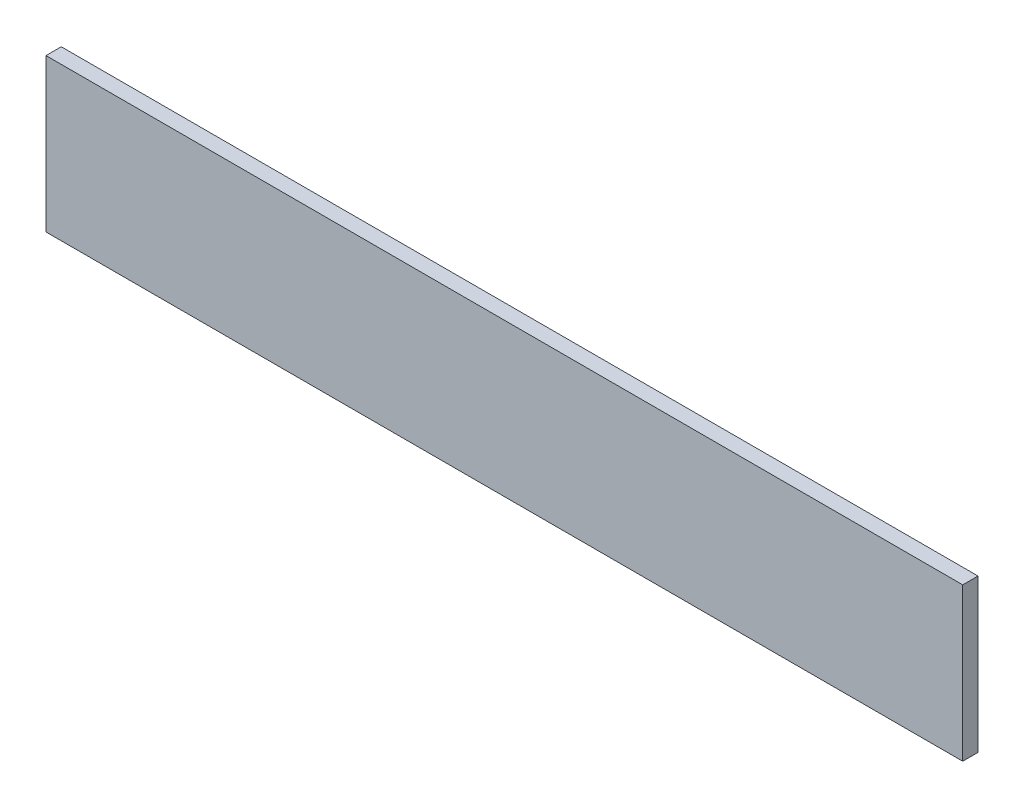
SolidWorks part; units mm, degrees
ref_plane "Спереди" through (0, 0, 0) normal (0, 0, 1) x (1, 0, 0)
ref_plane "Сверху" through (0, 0, 0) normal (0, 1, 0) x (1, 0, 0)
ref_plane "Справа" through (0, 0, 0) normal (1, 0, 0) x (0, 0, -1)
sketch "Эскиз1" plane through (0, 0, 0) normal (0, 0, 1) x (1, 0, 0)
  line L1 (0, 0) -> (120, 0)
  line L2 (0, 0) -> (0, -20)
  line L3 (0, -20) -> (120, -20)
  line L4 (120, 0) -> (120, -20)
  dimension "D1" = 120
extrude "Бобышка-Вытянуть1" add sketch "Эскиз1" along normal blind 2
sketch "Сгиб-Линии1" [suppressed] plane through (0, 0, 0) normal (0, 1, 0) x (1, 0, 0)
sketch "Граничная рамка1" [suppressed] plane through (0, 0, 0) normal (0, 1, 0) x (1, 0, 0)
